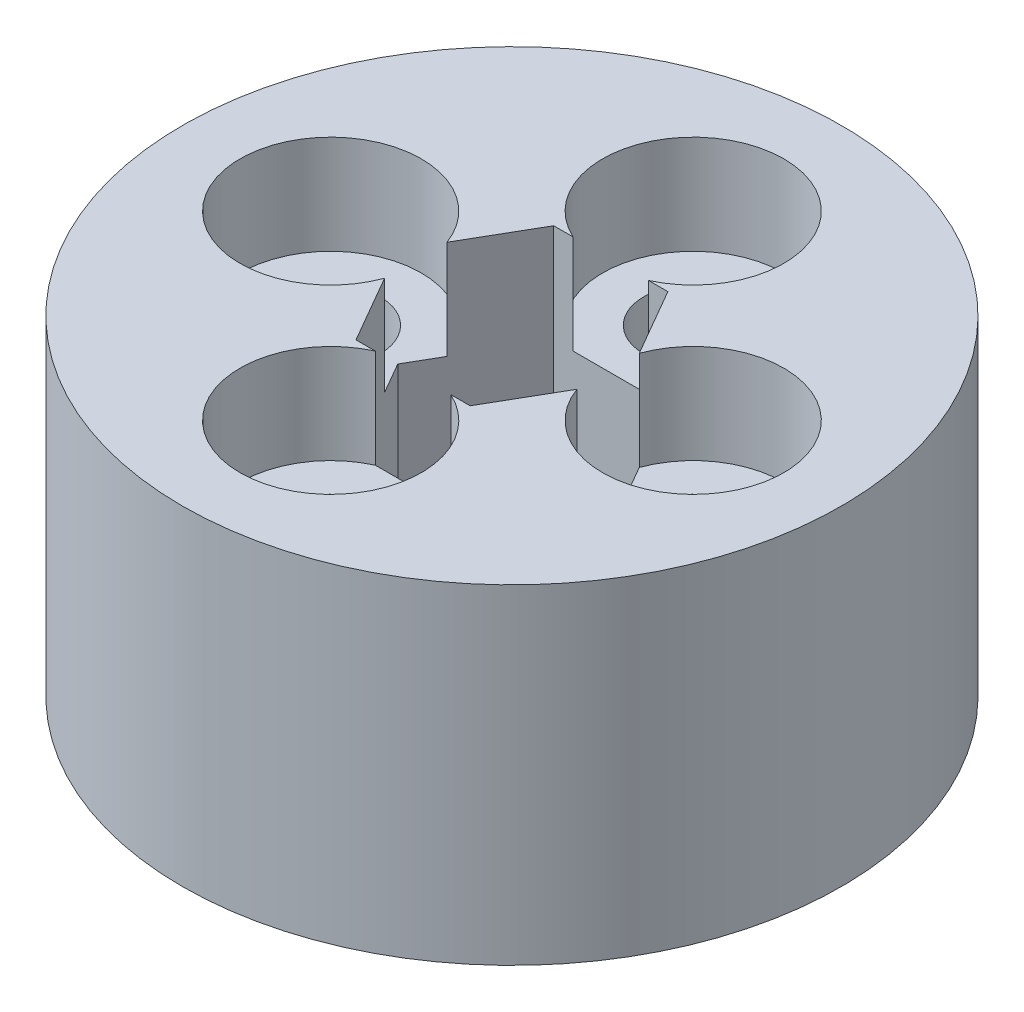
SolidWorks part; units mm, degrees
ref_plane "Front Plane" through (0, 0, 0) normal (0, 0, 1) x (1, 0, 0)
ref_plane "Top Plane" through (0, 0, 0) normal (0, 1, 0) x (1, 0, 0)
ref_plane "Right Plane" through (0, 0, 0) normal (1, 0, 0) x (0, 0, -1)
sketch "Sketch1" plane through (0, 0, 0) normal (0, 1, 0) x (1, 0, 0)
  circle A0 centre (0, 0) radius 10
  circle A1 centre (0, 5.5) radius 1.5
  circle A2 centre (5.5, 0) radius 1.5
  circle A3 centre (0, -5.5) radius 1.5
  circle A4 centre (-5.5, 0) radius 1.5
  point P14 (0, 0)
  dimension "D1" = 20
  dimension "D3" = 3
  dimension "D2" = 5.5
  dimension "D4" = 4
extrude "Boss-Extrude1" add sketch "Sketch1" along normal blind 10
sketch "Sketch2" plane through (0, 10, 0) normal (0, 1, 0) x (1, 0, 0)
  circle A0 centre (0, 5.5) radius 2.75
  circle A1 centre (5.5, 0) radius 2.75
  circle A2 centre (0, -5.5) radius 2.75
  circle A3 centre (-5.5, 0) radius 2.75
  point P12 (0, 0)
  dimension "D1" = 5.5
  dimension "D2" = 4
extrude "Cut-Extrude1" cut sketch "Sketch2" against normal blind 3
sketch "Sketch3" plane through (0, 10, 0) normal (0, 1, 0) x (1, 0, 0)
  line L1 (3.4641, 0) -> (1.7321, 3)
  line L2 (1.7321, 3) -> (-1.7321, 3)
  line L3 (-1.7321, 3) -> (-3.4641, 0)
  line L4 (-3.4641, 0) -> (-1.7321, -3)
  line L5 (-1.7321, -3) -> (1.7321, -3)
  line L6 (1.7321, -3) -> (3.4641, 0)
  circle A0 centre (0, 0) radius 3 construction
  dimension "D1" = 6
extrude "Cut-Extrude2" cut sketch "Sketch3" against normal blind 7
